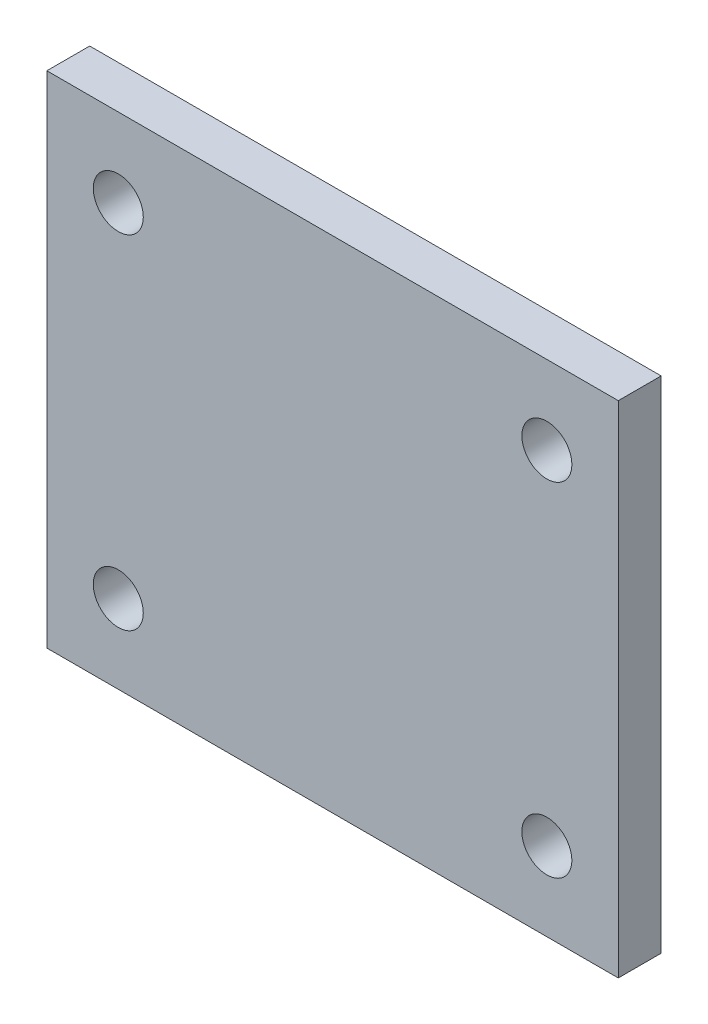
SolidWorks part; units mm, degrees
ref_plane "Front Plane" through (0, 0, 0) normal (0, 0, 1) x (1, 0, 0)
ref_plane "Top Plane" through (0, 0, 0) normal (0, 1, 0) x (1, 0, 0)
ref_plane "Right Plane" through (0, 0, 0) normal (1, 0, 0) x (0, 0, -1)
sketch "Sketch1" plane through (0, 0, 0) normal (0, 0, 1) x (1, 0, 0)
  line L1 (0, 0) -> (40, 0)
  line L2 (0, 0) -> (0, 35)
  line L3 (0, 35) -> (40, 35)
  line L4 (40, 0) -> (40, 35)
  line L5 (5, 29.5) -> (35, 29.5) construction
  line L6 (5, 29.5) -> (5, 5.5) construction
  line L7 (5, 5.5) -> (35, 5.5) construction
  line L8 (35, 29.5) -> (35, 5.5) construction
  line L9 (5, 29.5) -> (35, 5.5) construction
  line L10 (5, 5.5) -> (35, 29.5) construction
  circle A0 centre (5, 29.5) radius 1.75
  circle A1 centre (5, 5.5) radius 1.75
  circle A2 centre (35, 5.5) radius 1.75
  circle A3 centre (35, 29.5) radius 1.75
  point P5 (20, 17.5)
  point P10 (20, 29.5)
  point P11 (20, 35)
  point P13 (0, 17.5)
  dimension "D1" = 3.5
  dimension "D2" = 30
  dimension "D3" = 24
  dimension "D4" = 40
  dimension "D5" = 35
extrude "Boss-Extrude1" add sketch "Sketch1" along normal blind 3
